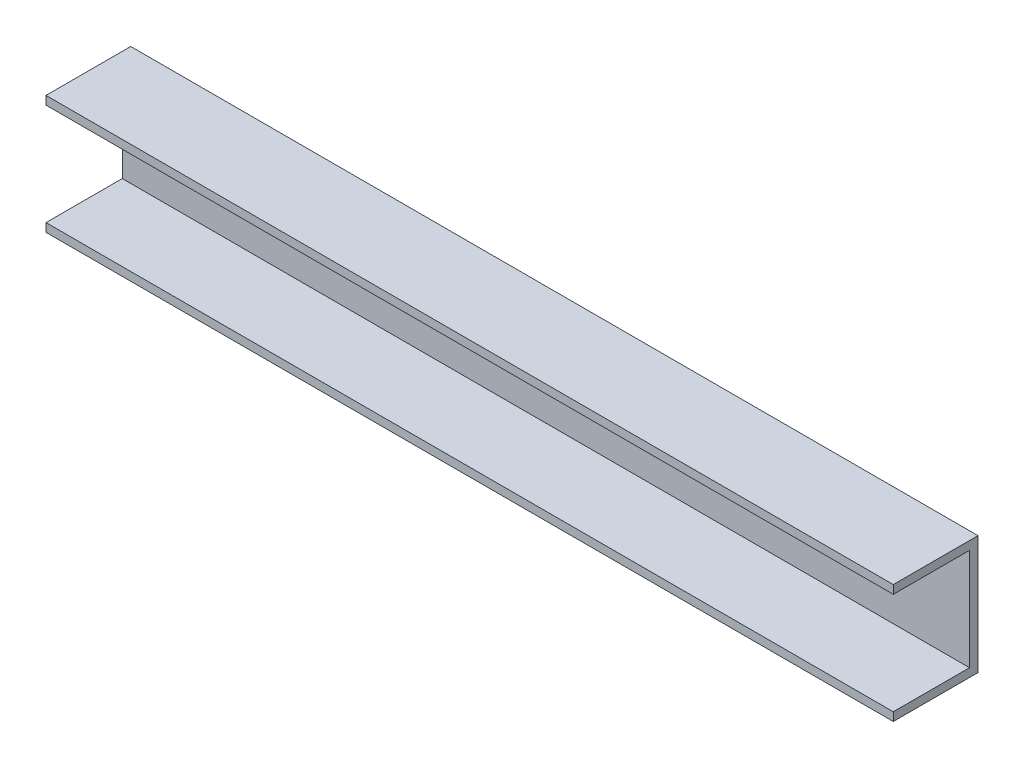
SolidWorks part; units mm, degrees
ref_plane "Front Plane" through (0, 0, 0) normal (0, 0, 1) x (1, 0, 0)
ref_plane "Top Plane" through (0, 0, 0) normal (0, 1, 0) x (1, 0, 0)
ref_plane "Right Plane" through (0, 0, 0) normal (1, 0, 0) x (0, 0, -1)
sketch "Sketch1" plane through (0, 0, 0) normal (1, 0, 0) x (0, 0, -1)
  line L0 (-33.9593, 53.0102) -> (16.0407, 53.0102)
  line L1 (16.0407, 53.0102) -> (16.0407, -16.9898)
  line L2 (16.0407, -16.9898) -> (-33.9593, -16.9898)
  line L3 (-33.9593, -16.9898) -> (-33.9593, -11.9898)
  line L4 (-33.9593, -11.9898) -> (11.0407, -11.9898)
  line L5 (11.0407, -11.9898) -> (11.0407, 48.0102)
  line L6 (11.0407, 48.0102) -> (-33.9593, 48.0102)
  line L7 (-33.9593, 48.0102) -> (-33.9593, 53.0102)
  dimension "D1" = 70
  dimension "D2" = 60
  dimension "D3" = 5
  dimension "D4" = 50
  dimension "D5" = 5
extrude "Boss-Extrude1" add sketch "Sketch1" along normal mid plane 500
